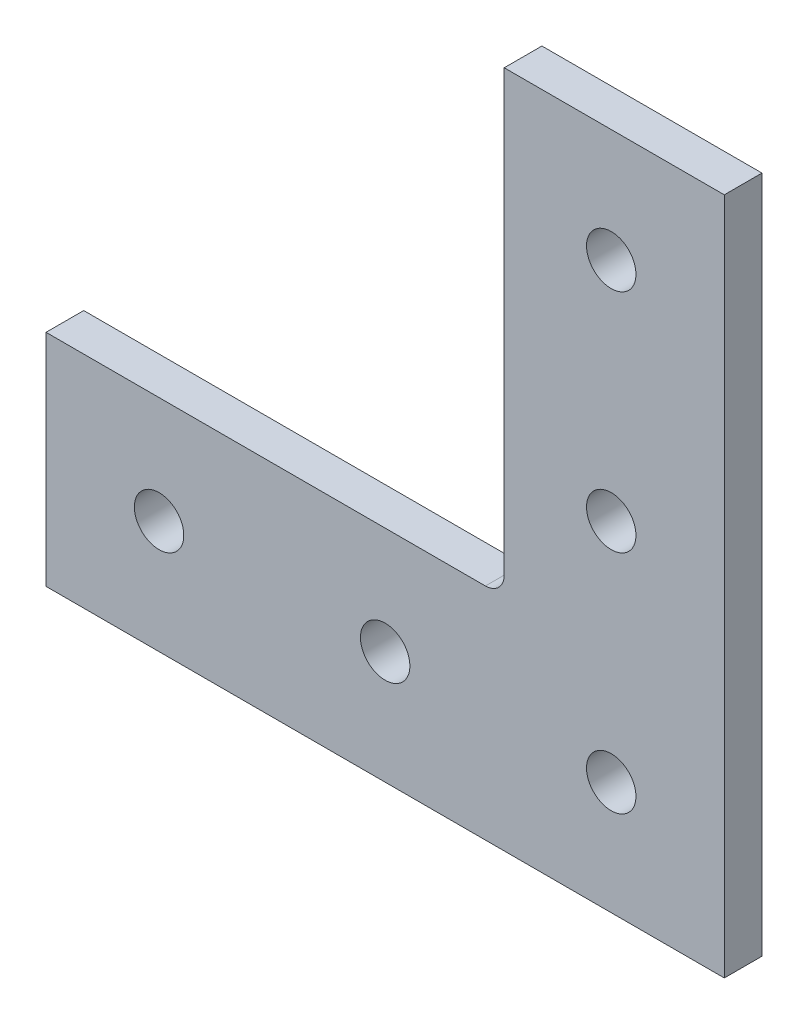
SolidWorks part; units mm, degrees
ref_plane "Front Plane" through (0, 0, 0) normal (0, 0, 1) x (1, 0, 0)
ref_plane "Top Plane" through (0, 0, 0) normal (0, 1, 0) x (1, 0, 0)
ref_plane "Right Plane" through (0, 0, 0) normal (1, 0, 0) x (0, 0, -1)
ref_plane "Plane1" through (0, 0, 6.35) normal (0, 0, 1) x (1, 0, 0)
sketch "Sketch1" plane through (0, 0, 6.35) normal (0, 0, 1) x (1, 0, 0)
  line L0 (-40.259, 37.084) -> (-114.3, 37.084)
  line L1 (-114.3, 37.084) -> (-114.3, 0)
  line L2 (-114.3, 0) -> (0, 0)
  line L3 (0, 0) -> (0, 114.3)
  line L4 (0, 114.3) -> (-37.084, 114.3)
  line L5 (-37.084, 114.3) -> (-37.084, 40.259)
  circle A0 centre (-95.25, 19.05) radius 4.1656
  circle A1 centre (-57.15, 19.05) radius 4.1656
  circle A2 centre (-19.05, 57.15) radius 4.1656
  circle A3 centre (-19.05, 95.25) radius 4.1656
  circle A4 centre (-19.05, 19.05) radius 4.1656
  arc A5 (-37.084, 40.259) -> (-40.259, 37.084) centre (-40.259, 40.259) cw
extrude "Boss-Extrude1" add sketch "Sketch1" against normal blind 6.35
